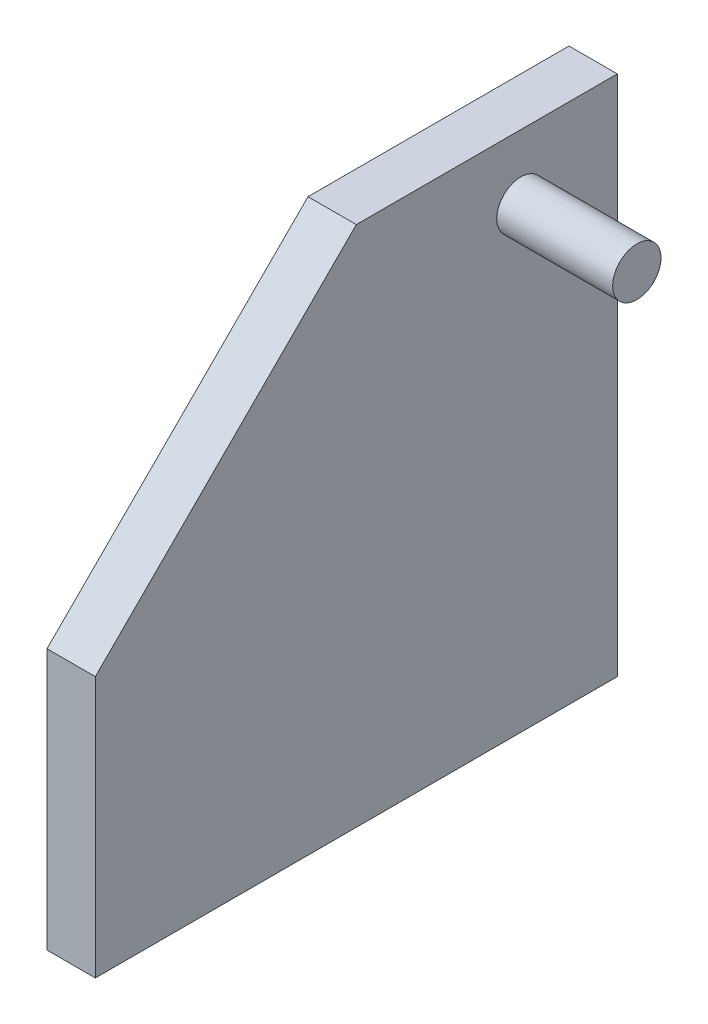
SolidWorks part; units mm, degrees
ref_plane "Front Plane" through (0, 0, 0) normal (0, 0, 1) x (1, 0, 0)
ref_plane "Top Plane" through (0, 0, 0) normal (0, 1, 0) x (1, 0, 0)
ref_plane "Right Plane" through (0, 0, 0) normal (1, 0, 0) x (0, 0, -1)
sketch "Sketch1" plane through (0, 0, 0) normal (1, 0, 0) x (0, 0, -1)
  line L1 (-42.271, -18.9761) -> (-15.271, -18.9761)
  line L2 (-42.271, -18.9761) -> (-42.271, 8.0239)
  line L3 (-42.271, 8.0239) -> (-15.271, 8.0239)
  line L4 (-15.271, -18.9761) -> (-15.271, 8.0239)
  dimension "D1" = 27
  dimension "D2" = 27
extrude "Boss-Extrude1" add sketch "Sketch1" along normal blind 2.5
sketch "Sketch2" plane through (2.5, 0, 0) normal (1, 0, 0) x (0, 0, -1)
  line L0 (-42.271, -18.9761) -> (-15.271, -18.9761) construction
  line L1 (-42.271, 8.0239) -> (-42.271, -18.9761) construction
  circle A0 centre (-20.261, 4.6539) radius 1.25
  dimension "D1" = 23.63
  dimension "D2" = 22.01
extrude "Boss-Extrude2" add sketch "Sketch2" along normal blind 6
sketch "Sketch3" plane through (0, 0, 0) normal (-1, 0, 0) x (0, 0, 1)
  line L0 (42.271, -18.9761) -> (15.271, -18.9761) construction
  line L1 (22.271, -18.9761) -> (32.271, -18.9761)
  line L2 (22.271, -18.9761) -> (22.271, -12.9761)
  line L3 (22.271, -12.9761) -> (32.271, -12.9761)
  line L4 (32.271, -18.9761) -> (32.271, -12.9761)
  dimension "D1" = 10
  dimension "D2" = 6
  dimension "D3" = 10
extrude "Boss-Extrude3" add sketch "Sketch3" along normal blind 7
sketch "Sketch4" plane through (2.5, 0, 0) normal (1, 0, 0) x (0, 0, -1)
  line L0 (-42.271, -5.4761) -> (-28.771, 8.0239)
  line L1 (-42.271, 8.0239) -> (-42.271, -18.9761) construction
  line L2 (-15.271, 8.0239) -> (-42.271, 8.0239) construction
  line L3 (-28.771, 8.0239) -> (-42.271, 8.0239)
  line L4 (-42.271, 8.0239) -> (-42.271, -5.4761)
extrude "Cut-Extrude1" cut sketch "Sketch4" against normal through all
